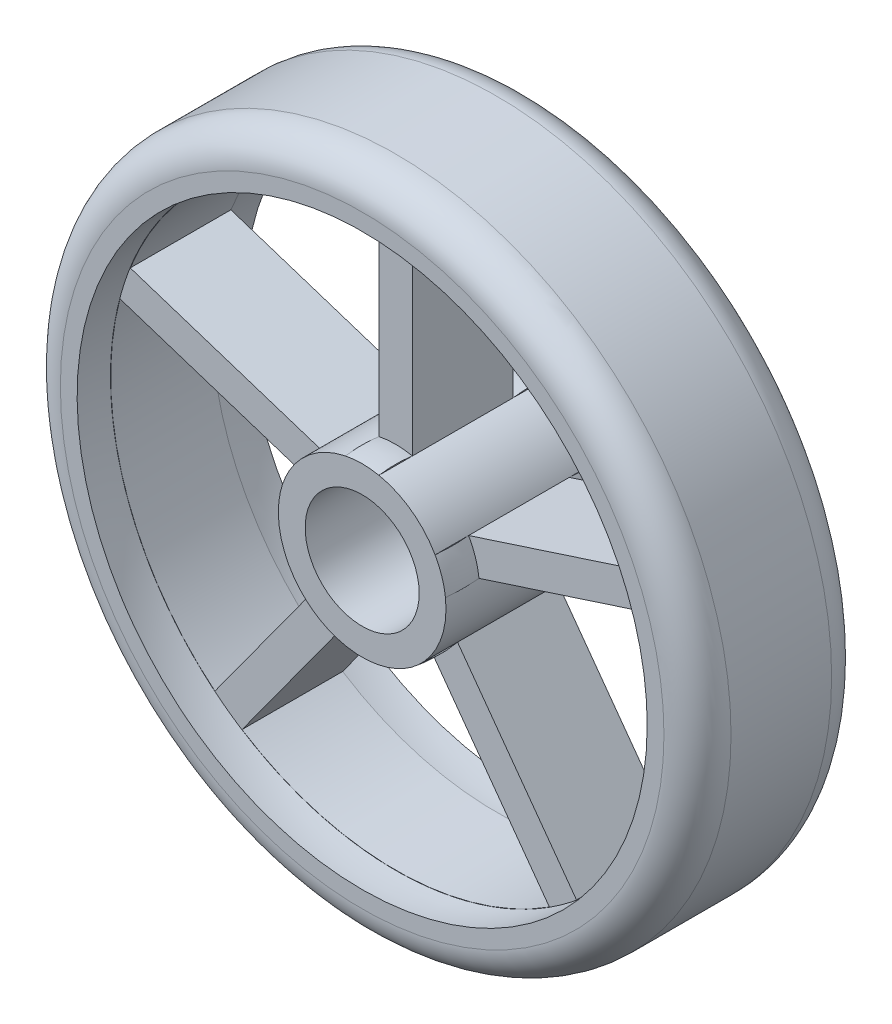
SolidWorks part; units mm, degrees
ref_plane "Front Plane" through (0, 0, 0) normal (0, 0, 1) x (1, 0, 0)
ref_plane "Top Plane" through (0, 0, 0) normal (0, 1, 0) x (1, 0, 0)
ref_plane "Right Plane" through (0, 0, 0) normal (1, 0, 0) x (0, 0, -1)
sketch "Sketch1" plane through (0, 0, 0) normal (0, 0, 1) x (1, 0, 0)
  line L0 (-1, 3.2496) -> (-1, 1.3764)
  line L1 (1, 3.2496) -> (1, 1.3764)
  line L2 (0, 0) -> (0, 3.4) construction
  line L3 (-3.6886, -3.3756) -> (-10.7841, -13.1417)
  line L4 (0.9985, 1.3759) -> (1, 1.3764)
  line L5 (1.6171, -0.5244) -> (1.618, -0.5257)
  line L6 (0.0009, -1.7) -> (0, -1.7013)
  line L7 (-1.6165, -0.5262) -> (-1.618, -0.5257)
  line L8 (1.6165, -0.5262) -> (1.618, -0.5257)
  line L9 (-0.0009, -1.7) -> (0, -1.7013)
  line L10 (-1.6171, -0.5244) -> (-1.618, -0.5257)
  line L11 (-0.9985, 1.3759) -> (-1, 1.3764)
  line L12 (-4.9682, 0.5628) -> (-16.449, 4.2931)
  line L13 (-4.3502, 2.4649) -> (-15.8309, 6.1952)
  line L14 (-1, 4.899) -> (-1, 16.9706)
  line L15 (1, 4.899) -> (1, 16.9706)
  line L16 (4.3502, 2.4649) -> (15.8309, 6.1952)
  line L17 (4.9682, 0.5628) -> (16.449, 4.2931)
  line L18 (3.6886, -3.3756) -> (10.7841, -13.1417)
  line L19 (2.0705, -4.5511) -> (9.166, -14.3173)
  line L20 (-2.0705, -4.5511) -> (-9.166, -14.3173)
  circle A0 centre (0, 0) radius 3.4
  circle A1 centre (0, 0) radius 20
  arc A2 (-16.449, 4.2931) -> (-10.7841, -13.1417) centre (0, 0) ccw
  arc A3 (15.8309, 6.1952) -> (1, 16.9706) centre (0, 0) ccw
  arc A4 (-1, 16.9706) -> (-15.8309, 6.1952) centre (0, 0) ccw
  circle A5 centre (0, 0) radius 5
  arc A6 (-9.166, -14.3173) -> (9.166, -14.3173) centre (0, 0) ccw
  arc A7 (10.7841, -13.1417) -> (16.449, 4.2931) centre (0, 0) ccw
  point P23 (0, 0)
  point P32 (0, 0)
  dimension "D1" = 40
  dimension "D2" = 6.8
  dimension "D3" = 34
  dimension "D8" = 10
  dimension "D4" = 1
  dimension "D5" = 1
  dimension "D6" = 5
  dimension "D7" = 5
extrude "Boss-Extrude4" add sketch "Sketch1" along normal blind 10 contours A1 A7 L18 A5 L19 A6 L20 L3 A2 L12 L13 A4 L14 L15 A3 L16 L17 | A5 A0 L4 L1 L5 L8 L6 L9 L7 L10 L0 L11
fillet "Fillet1" radius 2 2 edges at (20, 0, 10) (20, 0, 0)
sketch "Sketch3" plane through (1, 0, 0) normal (1, 0, 0) x (0, 0, -1)
  line L0 (-8, -20) -> (-8, 20) construction
  line L2 (-10, 16.9706) -> (-10, 4.899)
  line L4 (-8, 16.9805) -> (-8, 4.899)
  line L5 (-10, 4.899) -> (0, 4.899) construction
  line L6 (-2, 20) -> (-2, -20) construction
  line L8 (0, 16.9706) -> (0, 4.899)
  line L10 (-2, 16.9706) -> (-2, 4.899)
  arc A0 (-10, 16.9706) -> (-8, 16.9805) centre (-8.9399, 4.9171) cw
  arc A1 (-2, 16.9706) -> (0, 16.9706) centre (-1, 4.912) cw
  arc A2 (-10, 4.899) -> (-8, 4.899) centre (-9, -1.8271) cw
  arc A3 (-2, 4.899) -> (0, 4.899) centre (-1, -1.8271) cw
sweep "Cut-Sweep1" cut profiles "Sketch3" path edge at (18, 0, 0)
